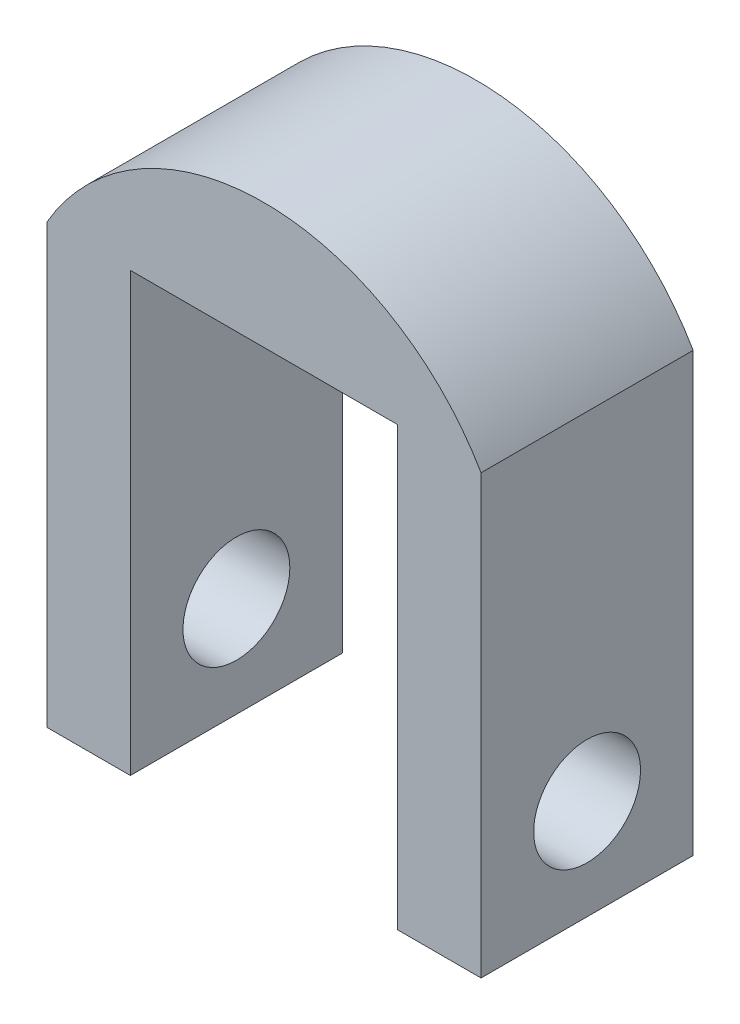
SolidWorks part; units mm, degrees
ref_plane "Front Plane" through (0, 0, 0) normal (0, 0, 1) x (1, 0, 0)
ref_plane "Top Plane" through (0, 0, 0) normal (0, 1, 0) x (1, 0, 0)
ref_plane "Right Plane" through (0, 0, 0) normal (1, 0, 0) x (0, 0, -1)
sketch "Sketch1" plane through (0, 0, 0) normal (0, 0, 1) x (1, 0, 0)
  line L0 (0, 0) -> (0, 26.2)
  line L1 (-26, 26.2) -> (-26, 0)
  line L2 (-26, 0) -> (-21, 0)
  line L3 (-21, 0) -> (-21, 26.2)
  line L4 (-5, 26.2) -> (-5, 0)
  line L5 (-5, 0) -> (0, 0)
  line L6 (-21, 26.2) -> (-5, 26.2)
  arc A0 (0, 26.2) -> (-26, 26.2) centre (-13, 18.7167) ccw
  point P5 (-13, 26.2)
  dimension "D1" = 16
  dimension "D3" = 26.2
  dimension "D4" = 15
  dimension "D2" = 5
extrude "Boss-Extrude1" add sketch "Sketch1" along normal blind 12.7
sketch "Sketch2" plane through (0, 0, 0) normal (1, 0, 0) x (0, 0, -1)
  line L0 (-12.7, 0) -> (0, 0) construction
  circle A0 centre (-6.35, 6) radius 3.2
  point P4 (-6.35, 0)
  dimension "D1" = 6.4
  dimension "D2" = 6
extrude "Cut-Extrude1" cut sketch "Sketch2" against normal through all
